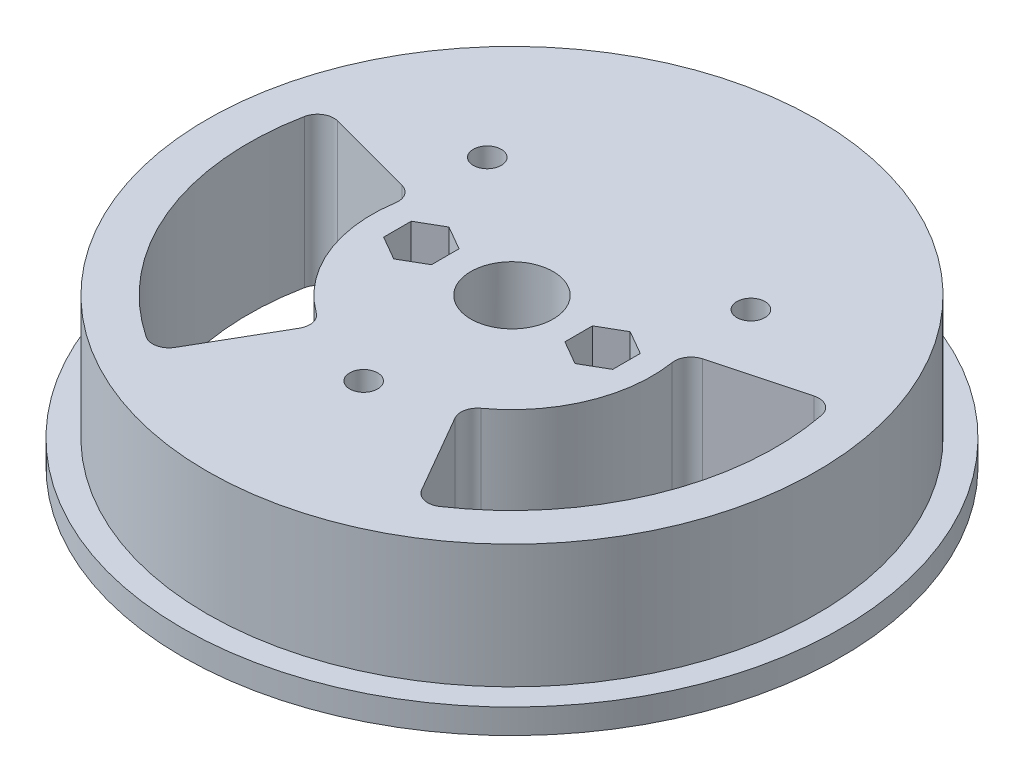
SolidWorks part; units mm, degrees
material "PLA"
ref_plane "Alzado" through (0, 0, 0) normal (0, 0, 1) x (1, 0, 0)
ref_plane "Planta" through (0, 0, 0) normal (0, 1, 0) x (1, 0, 0)
ref_plane "Vista lateral" through (0, 0, 0) normal (1, 0, 0) x (0, 0, -1)
sketch "Croquis1" plane through (0, 0, 0) normal (0, 0, 1) x (1, 0, 0)
  line L0 (0, 0) -> (40, 0)
  line L1 (40, 0) -> (40, 3)
  line L2 (40, 3) -> (37, 3)
  line L3 (37, 3) -> (37, 18)
  line L4 (37, 18) -> (0, 18)
  line L5 (0, 18) -> (0, 0)
  dimension "D1" = 37
  dimension "D2" = 40
  dimension "D3" = 3
  dimension "D4" = 15
revolve "Revolución1" add sketch "Croquis1" angle 360 about L5
sketch "Croquis2" plane through (0, 0, 0) normal (0, -1, 0) x (1, 0, 0)
  line L0 (-11.5, -19.5) -> (11.5, -19.5)
  line L1 (11.5, -19.5) -> (11.5, -23)
  line L2 (11.5, -23) -> (5, -29.5)
  line L3 (5, -29.5) -> (5, -54.5)
  line L4 (5, -54.5) -> (2.5, -54.5)
  line L5 (2.5, -54.5) -> (2.5, -29.5)
  line L6 (2.5, -29.5) -> (9, -23)
  line L7 (9, -23) -> (-9, -23)
  line L8 (-9, -23) -> (-2.5, -29.5)
  line L9 (-2.5, -29.5) -> (-2.5, -54.5)
  line L10 (-2.5, -54.5) -> (-5, -54.5)
  line L11 (-5, -54.5) -> (-5, -29.5)
  line L12 (-5, -29.5) -> (-11.5, -23)
  line L13 (-11.5, -23) -> (-11.5, -19.5)
  point P2 (0, -19.5)
  point P15 (0, -23)
  dimension "D1" = 3.5
  dimension "D2" = 2.5
  dimension "D3" = 45
  dimension "D4" = 45
  dimension "D5" = 5
  dimension "D6" = 6.5
  dimension "D7" = 19.5
  dimension "D8" = 25
extrude "Cortar-Extruir1" cut sketch "Croquis2" against normal blind 13
ref_plane "Plano1" through (0, 0, -40) normal (0, 0, 1) x (1, 0, 0)
sketch "Croquis3" plane through (0, 0, -40) normal (0, 0, 1) x (1, 0, 0)
  circle A0 centre (0, 6.5) radius 1.7
  dimension "D2" = 3.4
  dimension "D1" = 6.5
extrude "Cortar-Extruir2" cut sketch "Croquis3" along normal up to surface (17 mm away) up to face at (0, 6.5, -23)
ref_plane "Plano2" through (0, 0, -25.85) normal (0, 0, 1) x (1, 0, 0)
sketch "Croquis4" plane through (0, 0, -25.85) normal (0, 0, 1) x (1, 0, 0)
  line L0 (2.5, 13) -> (2.5, 3) construction
  line L1 (0, 9.85) -> (-2.9012, 8.175)
  line L2 (-2.9012, 8.175) -> (-2.9012, 4.825)
  line L3 (-2.9012, 4.825) -> (0, 3.15) construction
  line L4 (0, 3.15) -> (2.9012, 4.825) construction
  line L5 (2.9012, 4.825) -> (2.9012, 8.175)
  line L6 (2.9012, 8.175) -> (0, 9.85)
  line L7 (-2.9012, 4.825) -> (-2.9012, -1.825)
  line L8 (-2.9012, -1.825) -> (2.9012, -1.825)
  line L9 (2.9012, -1.825) -> (2.9012, 4.825)
  circle A0 centre (0, 6.5) radius 3.35 construction
  dimension "D2" = 6.7
  dimension "D1" = 10
extrude "Cortar-Extruir3" cut sketch "Croquis4" against normal blind 1.5 and the other way blind 1.5
sketch "Croquis5" plane through (0, 18, 0) normal (0, 1, 0) x (1, 0, 0)
  circle A0 centre (0, 0) radius 5
  dimension "D1" = 10
extrude "Cortar-Extruir4" cut sketch "Croquis5" against normal up to surface (18 mm away) up to face at (0, 0, -17.9608)
sketch "Croquis6" plane through (0, 0, 0) normal (0, -1, 0) x (1, 0, 0)
  circle A0 centre (0, 0) radius 8.2
  dimension "D1" = 16.4
extrude "Cortar-Extruir5" cut sketch "Croquis6" against normal blind 9
sketch "Croquis7" plane through (0, 0, 0) normal (0, -1, 0) x (1, 0, 0)
  line L1 (15.3, -3.5) -> (-15.3, -3.5)
  line L2 (15.3, -3.5) -> (15.3, 3.5)
  line L3 (15.3, 3.5) -> (-15.3, 3.5)
  line L4 (-15.3, -3.5) -> (-15.3, 3.5)
  line L5 (15.3, -3.5) -> (-15.3, 3.5) construction
  line L6 (15.3, 3.5) -> (-15.3, -3.5) construction
  point P0 (0, 0)
  dimension "D1" = 7
  dimension "D2" = 30.6
extrude "Cortar-Extruir6" cut sketch "Croquis7" against normal blind 4
sketch "Croquis8" plane through (0, 4, 0) normal (0, -1, 0) x (1, 0, 0)
  line L0 (-11, 0) -> (11, 0) construction
  circle A0 centre (-11, 0) radius 1.7
  circle A1 centre (11, 0) radius 1.7
  point P2 (0, 0)
  dimension "D1" = 3.4
  dimension "D2" = 22
extrude "Cortar-Extruir7" cut sketch "Croquis8" against normal up to surface (14 mm away) up to face at (0, 18, 5)
sketch "Croquis9" plane through (0, 18, 0) normal (0, 1, 0) x (1, 0, 0)
  line L0 (0, 12.1666) -> (0, -11.2589) construction
  line L1 (-11, 3.35) -> (-13.9012, 1.675)
  line L2 (-13.9012, 1.675) -> (-13.9012, -1.675)
  line L3 (-13.9012, -1.675) -> (-11, -3.35)
  line L4 (-11, -3.35) -> (-8.0988, -1.675)
  line L5 (-8.0988, -1.675) -> (-8.0988, 1.675)
  line L6 (-8.0988, 1.675) -> (-11, 3.35)
  line L7 (11, 3.35) -> (8.0988, 1.675)
  line L8 (8.0988, 1.675) -> (8.0988, -1.675)
  line L9 (8.0988, -1.675) -> (11, -3.35)
  line L10 (11, -3.35) -> (13.9012, -1.675)
  line L11 (13.9012, -1.675) -> (13.9012, 1.675)
  line L12 (13.9012, 1.675) -> (11, 3.35)
  circle A0 centre (-11, 0) radius 3.35 construction
  circle A1 centre (11, 0) radius 3.35 construction
  dimension "D1" = 6.7
extrude "Cortar-Extruir8" cut sketch "Croquis9" against normal blind 11
sketch "Croquis10" plane through (0, 0, 0) normal (0, -1, 0) x (1, 0, 0)
  line L0 (0, 0) -> (-40, 0) construction
  line L1 (0, 0) -> (38.637, -10.3528) construction
  line L2 (0, 0) -> (20, 34.641) construction
  line L3 (9.4472, 16.3631) -> (14.9666, 25.923)
  line L4 (18.2506, -4.8902) -> (28.9133, -7.7473)
  arc A0 (5, -39.6863) -> (-5, -39.6863) centre (0, 0) ccw construction
  arc A1 (16.7927, -2.647) -> (10.0025, 13.7459) centre (0, 0) ccw
  arc A2 (31.393, -6.2031) -> (17.8119, 26.5845) centre (0, 0) ccw
  arc A3 (28.9133, -7.7473) -> (31.393, -6.2031) centre (29.4309, -5.8154) ccw
  arc A4 (18.2506, -4.8902) -> (16.7927, -2.647) centre (18.7683, -2.9584) cw
  arc A5 (10.0025, 13.7459) -> (9.4472, 16.3631) centre (11.1793, 15.3631) cw
  arc A6 (14.9666, 25.923) -> (17.8119, 26.5845) centre (16.6987, 24.923) cw
  point P15 (30.9096, -8.2822)
  point P18 (16.4207, -4.3999)
  point P21 (8.5, 14.7224)
  point P24 (16, 27.7128)
  dimension "D3" = 17
  dimension "D4" = 32
  dimension "D5" = 2
  dimension "D1" = 165
  dimension "D2" = 75
extrude "Cortar-Extruir9" cut sketch "Croquis10" against normal up to surface (18 mm away) up to face at (-11, 18, 0)
mirror "Simetría1" about plane through (0, 0, 0) normal (1, 0, 0) of "Cortar-Extruir9"
sketch "Croquis11" plane through (0, 0, 0) normal (0, -1, 0) x (1, 0, 0)
  line L0 (-16, -13) -> (16, -13) construction
  circle A0 centre (-16, -13) radius 1.7
  circle A1 centre (16, -13) radius 1.7
  circle A2 centre (0, 18) radius 1.7
  point P6 (0, -13)
  dimension "D3" = 3.4
  dimension "D1" = 32
  dimension "D2" = 13
  dimension "D4" = 18
extrude "Cortar-Extruir10" cut sketch "Croquis11" against normal up to surface (18 mm away) up to face at (-19.2634, 18, 7.9792)
sketch "Croquis12" plane through (0, 0, 0) normal (0, -1, 0) x (1, 0, 0)
  circle A0 centre (-16, -13) radius 2.95
  circle A1 centre (16, -13) radius 2.95
  circle A2 centre (0, 18) radius 2.95
  dimension "D1" = 5.9
extrude "Cortar-Extruir11" cut sketch "Croquis12" against normal blind 3
